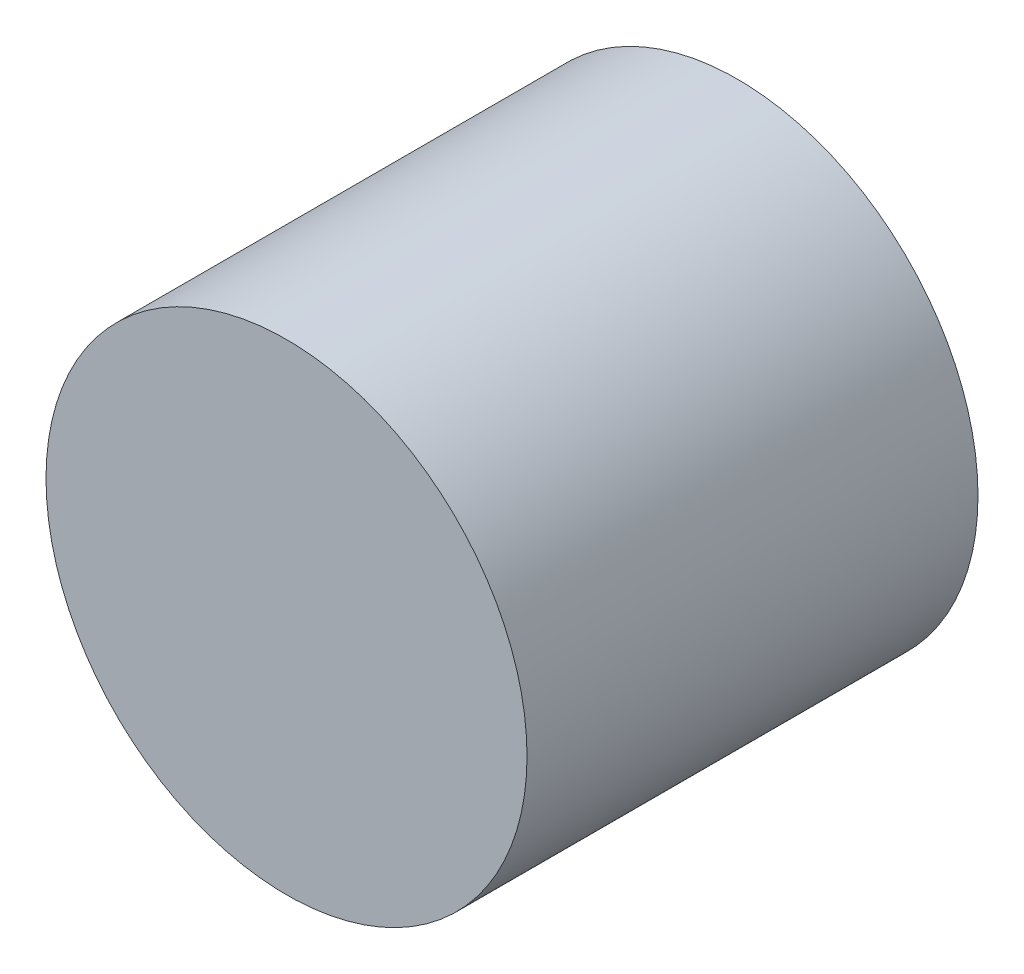
SolidWorks part; units mm, degrees
ref_plane "Plan de face" through (0, 0, 0) normal (0, 0, 1) x (1, 0, 0)
ref_plane "Plan de dessus" through (0, 0, 0) normal (0, 1, 0) x (1, 0, 0)
ref_plane "Plan de droite" through (0, 0, 0) normal (1, 0, 0) x (0, 0, -1)
sketch "Esquisse1" plane through (0, 0, 0) normal (0, 0, 1) x (1, 0, 0)
  circle A0 centre (0, 0) radius 80
  dimension "D1" = 160
extrude "Boss.-Extru.1" add sketch "Esquisse1" along normal blind 150
